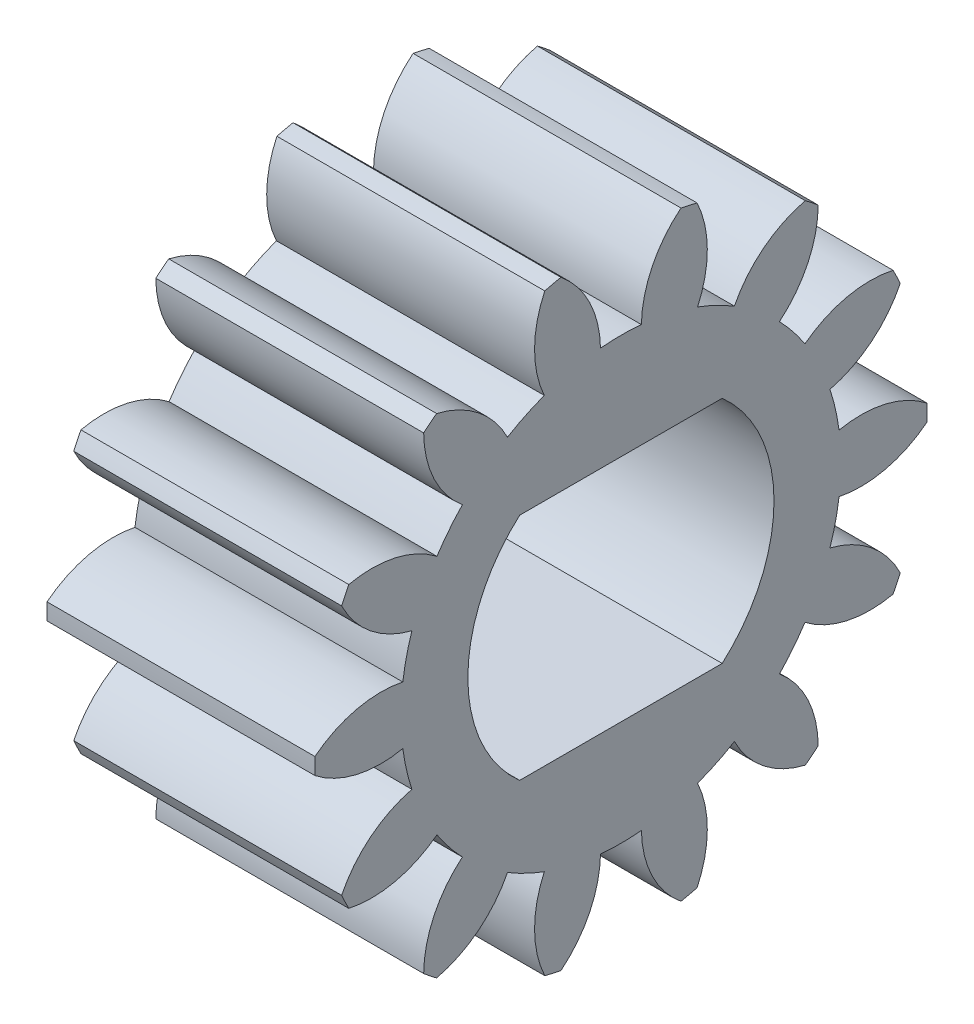
SolidWorks part; units mm, degrees
material "A286 Iron Base Superalloy"
ref_plane "Plane1" through (0, 0, 0) normal (0, 0, 1) x (1, 0, 0)
ref_plane "Plane2" through (0, 0, 0) normal (0, 1, 0) x (1, 0, 0)
ref_plane "Plane3" through (0, 0, 0) normal (1, 0, 0) x (0, 0, -1)
other "Configuration Table"
sketch "HoldingSke" plane through (0, 0, 0) normal (0, 1, 0) x (1, 0, 0)
  line L0 (0, 0) -> (0.4851, -0.121)
  line L1 (-15, 0) -> (100, 0) construction
  line L2 (0, 0) -> (-2.1039, 2.3779)
  line L3 (0, 0) -> (-11.863, 4.5341)
  line L4 (0, 0) -> (8.3795, 2.0892)
  line L5 (0, 0) -> (-46.8476, -17.4728)
  line L6 (0, 0) -> (-11.6055, -7.8303)
  line L7 (-2.1039, 2.3779) -> (8.6586, 51.2059)
  line L8 (-76.2, 54.61) -> (-76.1, 54.61)
  line L9 (-71.009, 38.7566) -> (-53.1078, 45.2721)
  line L10 (-76.2, 71.12) -> (104.1128, 71.12)
  line L11 (0, 0) -> (-14, 0)
  line L12 (-76.2, 101.6) -> (-76.133, 101.6)
  line L13 (24.9733, 27.94) -> (52.9518, 28.4284)
  line L14 (24.9733, 27.94) -> (24.9743, 27.94)
  line L15 (24.9733, 27.94) -> (100.4006, 29.5858)
  line L16 (-63.627, -2) -> (-12.827, -2)
  circle A0 centre (0, 0) radius 0.4
  circle A1 centre (0, 0) radius 11.499
  circle A2 centre (0, 0) radius 37.5
  circle A3 centre (0, 0) radius 0.4
  dimension "MHD" = 22.998
  dimension "Hub_dia" = 75
  dimension "Bore" = 0.8
  dimension "MBD" = 0.8
  dimension "Num_teeth" = 14
  dimension "Pitch" = 0.5
  dimension "Overall_len" = 50
  dimension "Show_teeth" = 14
  dimension "Thickness" = 14
  dimension "OAL" = 50.0001
  dimension "T_dim" = 0.1
  dimension "Ap" = 20
  dimension "H" = 19.05
  dimension "Pitch_radius" = 180.3128
  dimension "Width" = 14
  dimension "Backlash" = 0.067
  dimension "Addendum_fac" = 1
  dimension "Dedendum_fac" = 1.25
  dimension "Clearance_fac" = 0.25
  dimension "Dedendum_add" = 0.001
  dimension "Module" = 2
sketch "BasProSke" plane through (0, 0, 0) normal (0, 1, 0) x (1, 0, 0)
  line L0 (-10, 0) -> (60, 0) construction
  line L1 (0, 0) -> (0, 16)
  line L2 (0, 0) -> (14, 0)
  line L3 (14, 0) -> (14, 16)
  line L4 (14, 16) -> (0, 16)
  dimension "Thickness" = 14
  dimension "Diameter" = 32
revolve "Base-Revolve" add sketch "BasProSke" angle 360 about L0
sketch "TooCutSke" plane through (0, 0, 0) normal (1, 0, 0) x (0, 0, -1)
  line L1 (0, 0) -> (0, 107) construction
  line L2 (0, 0) -> (-1.6846, 13.8983) construction
  line L3 (0, 0) -> (-6.1971, 27.1511) construction
  line L4 (-1.6846, 13.8983) -> (-3.0985, 13.5756) construction
  arc A0 (1.0679, 11.4493) -> (-1.0679, 11.4493) centre (0, 0) ccw
  arc A1 (3.1634, 15.7101) -> (-3.1634, 15.7101) centre (0, 0) ccw
  circle A2 centre (0, 0) radius 14 construction
  circle A3 centre (0, 0) radius 13.1557 construction
  arc A4 (-1.0679, 11.4493) -> (-3.1634, 15.7101) centre (-6.6668, 11.3413) ccw
  arc A5 (3.1634, 15.7101) -> (1.0679, 11.4493) centre (6.6668, 11.3413) ccw
  dimension "Root_dia" = 22.998
  dimension "Overcut_dia" = 32.0508
  dimension "Pitch_dia" = 28
  dimension "Base_dia" = 26.3114
  dimension "Flank_rad" = 5.6
  dimension "Half_ang" = 12.857
  dimension "Half_CT" = 1.4503
extrude "ToothCut" cut sketch "TooCutSke" along normal through all
fillet "Breaks" [suppressed] radius 0.04
fillet "RootFillets" [suppressed] radius 0.501
pattern_circular "TeethCuts" count 14 every 25.714 about axis through (-10, 0, 0) along (1, 0, 0) of "ToothCut", "RootFillets", "Breaks"
sketch "HubNeaOneSke" plane through (0, 0, 0) normal (-1, 0, 0) x (0, 0, 1)
  circle A0 centre (0, 0) radius 11.499
  dimension "Diameter" = 22.998
extrude "HubNearOne" [suppressed] add sketch "HubNeaOneSke" along normal blind 36.0001
sketch "HubNeaBotSke" plane through (0, 0, 0) normal (-1, 0, 0) x (0, 0, 1)
  circle A0 centre (0, 0) radius 11.499
  dimension "Diameter" = 22.998
extrude "HubNearBoth" [suppressed] add sketch "HubNeaBotSke" along normal blind 18
ref_plane "FarPln" through (14, 0, 0) normal (1, 0, 0) x (0, 0, -1)
sketch "HubFarSke" plane through (14, 0, 0) normal (1, 0, 0) x (0, 0, -1)
  circle A0 centre (0, 0) radius 11.499
  dimension "Diameter" = 22.998
extrude "HubFar" [suppressed] add sketch "HubFarSke" along normal blind 18
sketch "BorSke" plane through (0, 0, 0) normal (1, 0, 0) x (0, 0, -1)
  circle A0 centre (0, 0) radius 0.4
  dimension "Diameter" = 0.8
extrude "Bore" cut sketch "BorSke" along normal mid plane 100.0001
sketch "KeySke" plane through (0, 0, 0) normal (1, 0, 0) x (0, 0, -1)
  line L0 (-0.05, 0) -> (-0.05, 0.5)
  line L1 (-0.05, 0.5) -> (0.05, 0.5)
  line L2 (0.05, 0.5) -> (0.05, 0)
  line L3 (0, 0) -> (0, 34) construction
  line L4 (-0.05, 0) -> (0.05, 0)
  dimension "Offset" = 0.5
  dimension "Width" = 0.1
extrude "Keyway" [suppressed] cut sketch "KeySke" along normal mid plane 100.0001
pattern_circular "Keyway2" [suppressed] count 2 every 90 about axis through (-10, 0, 0) along (1, 0, 0)
sketch "Sketch1" plane through (14, 0, 0) normal (1, 0, 0) x (0, 0, -1)
  line L0 (-5.2915, 6) -> (5.2915, 6)
  line L1 (-5.2915, -6) -> (5.2915, -6)
  arc A0 (-5.2915, 6) -> (-5.2915, -6) centre (0, 0) ccw
  arc A1 (5.2915, -6) -> (5.2915, 6) centre (0, 0) ccw
  dimension "D1" = 16
  dimension "D2" = 12
  dimension "D3" = 6
extrude "Cut-Extrude1" cut sketch "Sketch1" against normal through all
sketch "Sketch3" plane through (0, 0, 0) normal (0, 1, 0) x (1, 0, 0)
  line L0 (0, 0) -> (2.2898, 0)
  line L1 (0, 1.0679) -> (0, -1.0679) construction
  line L4 (-2.5414, 11.1099) -> (-2.5414, 0)
  line L5 (-2.5414, 0) -> (0, 0)
  line L6 (0, 0) -> (0, 10) construction
  line L7 (-21.4361, 0) -> (27.1716, 0) construction
  line L8 (2.2898, 0) -> (2.2898, 9)
  line L9 (2.2898, 9) -> (-2.5414, 11.1099)
  point P4 (-1.2707, 0)
  point P10 (2.2898, 9)
  dimension "D3" = 1.2707
  dimension "D1" = 9
  dimension "D2" = 10
  dimension "D4" = 4.8312
revolve "Cut-Revolve2" cut sketch "Sketch3" angle 360 about L7
equation "' \"Module@HoldingSke\" = 6.35"
equation "' \"Num_teeth@HoldingSke\" = 12"
equation "' \"Ap@HoldingSke\" =  20"
equation "' \"Ap@HoldingSke\" = 20"
equation "' \"Width@HoldingSke\" = 0.5 * 25.4"
equation "' \"Hub_dia@HoldingSke\"= 1 * 25.4"
equation "' \"Hub_dia@HoldingSke\" = 1 * 25.4"
equation "' \"Overall_len@HoldingSke\" = 1.0 * 25.4"
equation "' \"Bore@HoldingSke\" = 0.75 * 25.4"
equation "' \"T_dim@HoldingSke\" = 0.1 * 25.4"
equation "' \"Width@KeySke\" = 0.25 * 25.4"
equation "' \"Show_teeth@HoldingSke\" = 13"
equation "' \"Backlash@HoldingSke\" = 0.009 * 25.4"
equation "' \"Addendum_fac@HoldingSke\" = 1.0"
equation "' \"Dedendum_fac@HoldingSke\" = 1.25"
equation "' \"Dedendum_add@HoldingSke\" = 0.00005 * 25.4"
equation "' \"Clearance_fac@HoldingSke\" = 0.25"
equation "\"Pitch@HoldingSke\" = 1 / \"Module@HoldingSke\""
equation "\"Overcut_dia@TooCutSke\" = (\"Num_teeth@HoldingSke\" + 2 * \"Addendum_fac@HoldingSke\") / \"Pitch@HoldingSke\" + 0.002 * 25.4"
equation "\"Pitch_dia@TooCutSke\" = \"Num_teeth@HoldingSke\" / \"Pitch@HoldingSke\""
equation "\"Base_dia@TooCutSke\" = \"Num_teeth@HoldingSke\" / \"Pitch@HoldingSke\" * cos((\"Ap@HoldingSke\"  * 3.14159265 / 180))"
equation "\"Root_dia@TooCutSke\" = (\"Num_teeth@HoldingSke\" + 2) / \"Pitch@HoldingSke\" - 2 * (\"Addendum_fac@HoldingSke\" + \"Dedendum_fac@HoldingSke\") / \"Pitch@HoldingSke\" - \"Dedendum_add@HoldingSke\" * 2"
equation "\"Half_ang@TooCutSke\" = 180 / \"Num_teeth@HoldingSke\""
equation "\"Half_CT@TooCutSke\" = \"Num_teeth@HoldingSke\" / \"Pitch@HoldingSke\" * sin((3.14159265 / 2 / \"Num_teeth@HoldingSke\")) / 2 - 7 * \"Backlash@HoldingSke\" / 4"
equation "\"Flank_rad@TooCutSke\" = \"Num_teeth@HoldingSke\" / \"Pitch@HoldingSke\" / 5"
equation "\"Radius@RootFillets\" = \"Clearance_fac@HoldingSke\" / \"Pitch@HoldingSke\" + \"Dedendum_add@HoldingSke\""
equation "\"Break_rad@Breaks\" = 0.02 / \"Pitch@HoldingSke\""
equation "\"Thickness@HoldingSke\" = \"Width@HoldingSke\""
equation "\"OAL@HoldingSke\" = \"Thickness@HoldingSke\""
equation "\"MHD@HoldingSke\" = (\"Num_teeth@HoldingSke\" + 2) / \"Pitch@HoldingSke\" - 2 * (\"Addendum_fac@HoldingSke\" + \"Dedendum_fac@HoldingSke\")  / \"Pitch@HoldingSke\" - \"Dedendum_add@HoldingSke\" * 2"
equation "\"MBD@HoldingSke\" = (\"Num_teeth@HoldingSke\" + 2) / \"Pitch@HoldingSke\" - 2 * (\"Addendum_fac@HoldingSke\" + \"Dedendum_fac@HoldingSke\")  / \"Pitch@HoldingSke\" - \"Dedendum_add@HoldingSke\" * 2 - 0.002 * 25.4"
equation "\"MHD@HoldingSke\" = ((sgn( \"MHD@HoldingSke\" - \"Hub_dia@HoldingSke\" )-1)*( \"MHD@HoldingSke\" - \"Hub_dia@HoldingSke\" ))/-2+ \"Hub_dia@HoldingSke\""
equation "\"MBD@HoldingSke\" = ((sgn( \"MBD@HoldingSke\" - \"Bore@HoldingSke\" )-1)*( \"MBD@HoldingSke\" - \"Bore@HoldingSke\" ))/-2+ \"Bore@HoldingSke\""
equation "\"OAL@HoldingSke\" = ((sgn( \"OAL@HoldingSke\" - \"Overall_len@HoldingSke\" )+1)*( \"OAL@HoldingSke\" - \"Overall_len@HoldingSke\" ))/2 + \"Overall_len@HoldingSke\" + 0.000002 * 25.4"
equation "\"Num_teeth@TeethCuts\" = int( \"Show_teeth@HoldingSke\" ) + 1"
equation "\"Num_teeth@TeethCuts\" = ((sgn( \"Num_teeth@TeethCuts\" - \"Num_teeth@HoldingSke\" )-1)*( \"Num_teeth@TeethCuts\" - \"Num_teeth@HoldingSke\" ))/-2+ \"Num_teeth@HoldingSke\""
equation "\"Num_teeth@TeethCuts\" = ((sgn( \"Num_teeth@TeethCuts\" - 2.0)+1)*( \"Num_teeth@TeethCuts\" - 2.0))/2 +2.0"
equation "\"Angle@TeethCuts\" = 360.0 / \"Num_teeth@HoldingSke\""
equation "\"Diameter@BasProSke\" = (\"Num_teeth@HoldingSke\" + 2 * \"Addendum_fac@HoldingSke\") / \"Pitch@HoldingSke\""
equation "\"Thickness@BasProSke\"  = \"Thickness@HoldingSke\""
equation "' \"Fillet_rad@BasProSke\" =  \"Thickness@HoldingSke\" * 0.05"
equation "' \"Fillet_rad@BasProSke\" = \"Thickness@HoldingSke\" * 0.05"
equation "\"MHD@HoldingSke\" = ((sgn( \"MHD@HoldingSke\" - \"Root_dia@TooCutSke\" )-1)*( \"MHD@HoldingSke\" - \"Root_dia@TooCutSke\" ))/-2+ \"Root_dia@TooCutSke\""
equation "\"Diameter@HubNeaOneSke\" = \"MHD@HoldingSke\""
equation "\"Length@HubNearOne\" = \"OAL@HoldingSke\" - \"Thickness@BasProSke\""
equation "\"Diameter@HubNeaBotSke\" = \"MHD@HoldingSke\""
equation "\"Length@HubNearBoth\" = ( \"OAL@HoldingSke\" - \"Thickness@BasProSke\" ) / 2.0"
equation "\"Thickness@FarPln\" = \"Thickness@BasProSke\""
equation "\"Diameter@HubFarSke\" = \"MHD@HoldingSke\""
equation "\"Length@HubFar\" = ( \"OAL@HoldingSke\" - \"Thickness@BasProSke\" ) / 2.0"
equation "\"Diameter@BorSke\" = \"MBD@HoldingSke\""
equation "\"D1@Bore\" = \"OAL@HoldingSke\" * 2.0"
equation "\"D1@Keyway\" = \"OAL@HoldingSke\" * 2.0"
equation "\"Offset@KeySke\" = \"T_dim@HoldingSke\" + \"MBD@HoldingSke\" / 2.0"
